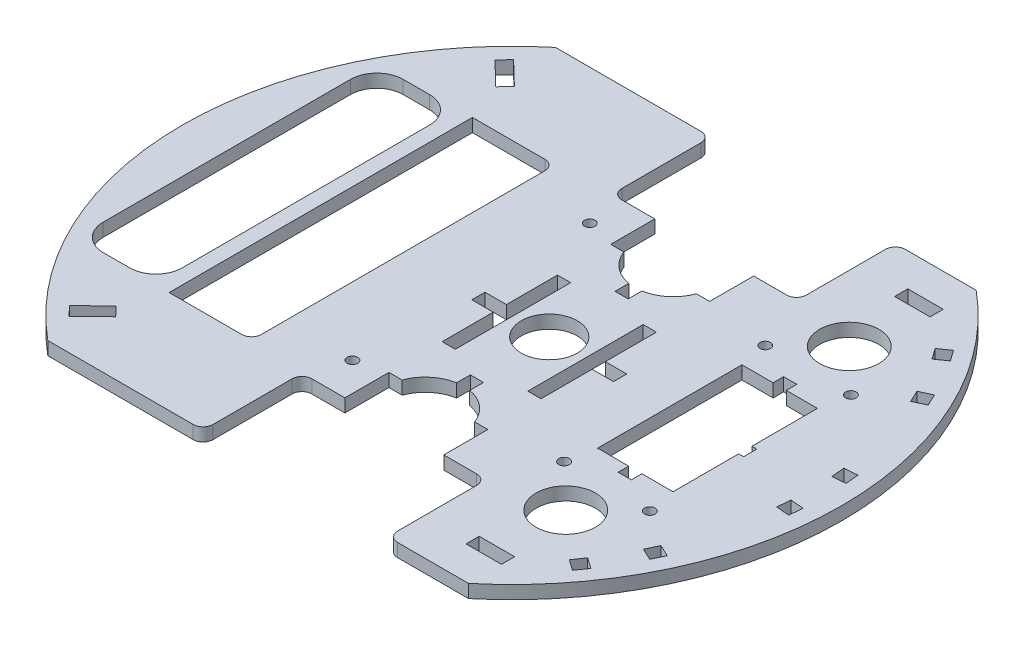
SolidWorks part; units mm, degrees
material "Oak"
ref_plane "Front Plane" through (0, 0, 0) normal (0, 0, 1) x (1, 0, 0)
ref_plane "Top Plane" through (0, 0, 0) normal (0, 1, 0) x (1, 0, 0)
ref_plane "Right Plane" through (0, 0, 0) normal (1, 0, 0) x (0, 0, -1)
sketch "Sketch1" plane through (0, 101.3337, 0) normal (0, 1, 0) x (1, 0, 0)
  line L0 (173.9372, -134.9612) -> (177.9372, -134.9612)
  line L2 (164.4872, -181.9612) -> (187.3872, -181.9612)
  line L3 (164.4872, -181.9612) -> (164.4872, -138.1612)
  line L12 (191.7991, -107.843) -> (195.0757, -105.5487)
  line L13 (189.5048, -104.5664) -> (191.7991, -107.843)
  line L14 (192.7814, -102.2721) -> (189.5048, -104.5664)
  line L15 (195.0757, -105.5487) -> (192.7814, -102.2721)
  line L16 (191.7991, -107.843) -> (195.0757, -105.5487)
  line L17 (189.5048, -104.5664) -> (191.7991, -107.843)
  line L18 (192.7814, -102.2721) -> (189.5048, -104.5664)
  line L19 (195.0757, -105.5487) -> (192.7814, -102.2721)
  line L28 (199.6807, -122.1917) -> (203.3059, -120.5012)
  line L29 (197.9902, -118.5664) -> (199.6807, -122.1917)
  line L30 (201.6155, -116.876) -> (197.9902, -118.5664)
  line L31 (203.3059, -120.5012) -> (201.6155, -116.876)
  line L32 (199.6807, -122.1917) -> (203.3059, -120.5012)
  line L33 (197.9902, -118.5664) -> (199.6807, -122.1917)
  line L34 (201.6155, -116.876) -> (197.9902, -118.5664)
  line L35 (203.3059, -120.5012) -> (201.6155, -116.876)
  line L68 (189.5048, -215.556) -> (192.7814, -217.8503)
  line L69 (191.7991, -212.2794) -> (189.5048, -215.556)
  line L70 (195.0757, -214.5737) -> (191.7991, -212.2794)
  line L71 (192.7814, -217.8503) -> (195.0757, -214.5737)
  line L72 (189.5048, -215.556) -> (192.7814, -217.8503)
  line L73 (191.7991, -212.2794) -> (189.5048, -215.556)
  line L74 (195.0757, -214.5737) -> (191.7991, -212.2794)
  line L75 (192.7814, -217.8503) -> (195.0757, -214.5737)
  line L84 (197.9902, -201.556) -> (201.6155, -203.2464)
  line L85 (199.6807, -197.9307) -> (197.9902, -201.556)
  line L86 (203.3059, -199.6212) -> (199.6807, -197.9307)
  line L87 (201.6155, -203.2464) -> (203.3059, -199.6212)
  line L88 (197.9902, -201.556) -> (201.6155, -203.2464)
  line L89 (199.6807, -197.9307) -> (197.9902, -201.556)
  line L90 (203.3059, -199.6212) -> (199.6807, -197.9307)
  line L91 (201.6155, -203.2464) -> (203.3059, -199.6212)
  line L116 (207.4498, -153.87) -> (211.4346, -153.5214)
  line L117 (207.1012, -149.8852) -> (207.4498, -153.87)
  line L118 (211.086, -149.5366) -> (207.1012, -149.8852)
  line L119 (211.4346, -153.5214) -> (211.086, -149.5366)
  line L120 (207.4498, -153.87) -> (211.4346, -153.5214)
  line L121 (207.1012, -149.8852) -> (207.4498, -153.87)
  line L122 (211.086, -149.5366) -> (207.1012, -149.8852)
  line L123 (211.4346, -153.5214) -> (211.086, -149.5366)
  line L124 (207.1012, -170.2372) -> (211.086, -170.5858)
  line L125 (207.4498, -166.2524) -> (207.1012, -170.2372)
  line L126 (211.4346, -166.601) -> (207.4498, -166.2524)
  line L127 (211.086, -170.5858) -> (211.4346, -166.601)
  line L128 (207.1012, -170.2372) -> (211.086, -170.5858)
  line L129 (207.4498, -166.2524) -> (207.1012, -170.2372)
  line L130 (211.4346, -166.601) -> (207.4498, -166.2524)
  line L131 (211.086, -170.5858) -> (211.4346, -166.601)
  line L256 (162.9372, -190.5612) -> (188.9372, -190.5612) construction
  line L257 (58.6296, -114.0612) -> (80.6296, -114.0612)
  line L258 (58.6296, -114.0612) -> (58.6296, -206.0612)
  line L259 (58.6296, -206.0612) -> (80.6296, -206.0612)
  line L260 (49.7, -227.4778) -> (56.8934, -220.5312)
  line L261 (46.9213, -224.6004) -> (49.7, -227.4778)
  line L262 (54.1147, -217.6539) -> (46.9213, -224.6004)
  line L263 (56.8934, -220.5312) -> (54.1147, -217.6539)
  line L268 (46.9213, -95.522) -> (54.1147, -102.4685)
  line L269 (49.7, -92.6446) -> (46.9213, -95.522)
  line L270 (56.8934, -99.5912) -> (49.7, -92.6446)
  line L271 (54.1147, -102.4685) -> (56.8934, -99.5912)
  line L272 (170.4372, -223.0612) -> (170.4372, -227.0612)
  line L273 (180.4372, -223.0612) -> (170.4372, -223.0612)
  line L274 (180.4372, -227.0612) -> (180.4372, -223.0612)
  line L275 (170.4372, -227.0612) -> (180.4372, -227.0612)
  line L276 (170.4372, -223.0612) -> (170.4372, -227.0612)
  line L277 (180.4372, -223.0612) -> (170.4372, -223.0612)
  line L278 (180.4372, -227.0612) -> (180.4372, -223.0612)
  line L279 (170.4372, -227.0612) -> (180.4372, -227.0612)
  line L280 (170.4372, -93.0612) -> (170.4372, -97.0612)
  line L281 (180.4372, -93.0612) -> (170.4372, -93.0612)
  line L282 (180.4372, -97.0612) -> (180.4372, -93.0612)
  line L283 (170.4372, -97.0612) -> (180.4372, -97.0612)
  line L284 (170.4372, -93.0612) -> (170.4372, -97.0612)
  line L285 (180.4372, -93.0612) -> (170.4372, -93.0612)
  line L286 (180.4372, -97.0612) -> (180.4372, -93.0612)
  line L287 (170.4372, -97.0612) -> (180.4372, -97.0612)
  line L288 (170.4372, -93.0612) -> (169.6872, -93.0612)
  line L299 (90.4372, -237.0612) -> (99.9372, -237.0612)
  line L302 (99.9372, -237.0612) -> (99.9372, -207.0612)
  line L303 (99.9372, -207.0612) -> (120.9039, -207.0612)
  line L336 (155.9372, -207.0612) -> (155.9372, -237.0612)
  line L352 (155.9372, -237.0612) -> (165.4372, -237.0612)
  line L353 (123.9372, -199.7112) -> (123.9372, -195.7112) construction
  line L354 (123.9372, -195.7112) -> (131.9372, -195.7112) construction
  line L355 (134.9705, -207.0612) -> (155.9372, -207.0612)
  line L356 (125.9372, -190.0112) -> (129.9372, -190.0112)
  line L357 (125.9372, -190.0112) -> (125.9372, -182.0112)
  line L358 (52.8284, -237.0612) -> (90.4372, -237.0612)
  line L359 (90.4372, -237.0612) -> (90.4372, -207.0612)
  line L360 (90.4372, -207.0612) -> (112.9372, -207.0612)
  line L361 (165.4372, -207.0612) -> (165.4372, -237.0612)
  line L362 (165.4372, -237.0612) -> (180.4372, -237.0612)
  line L363 (180.4372, -83.0612) -> (165.4372, -83.0612)
  line L364 (165.4372, -83.0612) -> (165.4372, -113.0612)
  line L365 (165.4372, -113.0612) -> (142.9372, -113.0612)
  line L366 (90.4372, -113.0612) -> (90.4372, -83.0612)
  line L367 (90.4372, -83.0612) -> (52.8284, -83.0612)
  line L368 (52.8284, -237.0612) -> (90.4372, -237.0612)
  line L369 (90.4372, -237.0612) -> (90.4372, -207.0612) construction
  line L370 (90.4372, -207.0612) -> (120.9039, -207.0612) construction
  line L371 (165.4372, -207.0612) -> (165.4372, -237.0612) construction
  line L372 (165.4372, -237.0612) -> (180.4372, -237.0612)
  line L373 (180.4372, -83.0612) -> (165.4372, -83.0612)
  line L374 (165.4372, -83.0612) -> (165.4372, -113.0612) construction
  line L375 (165.4372, -113.0612) -> (142.9372, -113.0612) construction
  line L376 (90.4372, -113.0612) -> (90.4372, -83.0612) construction
  line L377 (90.4372, -83.0612) -> (52.8284, -83.0612)
  line L378 (125.9372, -182.0112) -> (129.9372, -182.0112)
  line L379 (129.9372, -190.0112) -> (129.9372, -182.0112)
  line L380 (125.9372, -190.0112) -> (129.9372, -182.0112) construction
  line L381 (125.9372, -182.0112) -> (129.9372, -190.0112) construction
  line L382 (134.9705, -207.0612) -> (112.9372, -207.0612) construction
  line L383 (16.6328, -160.0612) -> (21.6328, -160.0612) construction
  line L384 (155.9372, -113.0612) -> (155.9372, -83.0612)
  line L385 (134.9705, -113.0612) -> (155.9372, -113.0612)
  line L386 (99.9372, -83.0612) -> (99.9372, -113.0612)
  line L387 (99.9372, -113.0612) -> (120.9039, -113.0612)
  line L388 (125.9372, -130.1112) -> (125.9372, -138.1112)
  line L389 (125.9372, -138.1112) -> (129.9372, -130.1112) construction
  line L390 (125.9372, -130.1112) -> (129.9372, -138.1112) construction
  line L391 (125.9372, -138.1112) -> (129.9372, -138.1112)
  line L392 (129.9372, -130.1112) -> (129.9372, -138.1112)
  line L393 (125.9372, -130.1112) -> (129.9372, -130.1112)
  line L394 (90.4372, -83.0612) -> (99.9372, -83.0612)
  line L395 (155.9372, -83.0612) -> (165.4372, -83.0612)
  line L396 (142.9372, -142.5612) -> (138.9372, -142.5612) construction
  line L397 (142.9372, -144.5612) -> (142.9372, -142.5612) construction
  line L398 (138.9372, -144.5612) -> (138.9372, -142.5612) construction
  line L400 (138.9372, -175.5612) -> (138.9372, -144.5612) construction
  line L401 (138.9372, -177.5612) -> (138.9372, -175.5612) construction
  line L402 (142.9372, -177.5612) -> (138.9372, -177.5612) construction
  line L403 (142.9372, -177.5612) -> (142.9372, -175.5612) construction
  line L404 (116.9372, -144.5612) -> (116.9372, -142.5612) construction
  line L405 (116.9372, -175.5612) -> (116.9372, -144.5612) construction
  line L406 (116.9372, -177.5612) -> (116.9372, -175.5612) construction
  line L407 (112.9372, -177.5612) -> (112.9372, -175.5612) construction
  line L409 (112.9372, -144.5612) -> (112.9372, -142.5612) construction
  line L410 (116.9372, -142.5612) -> (112.9372, -142.5612) construction
  line L411 (116.9372, -177.5612) -> (112.9372, -177.5612) construction
  line L412 (142.9372, -142.5612) -> (138.9372, -142.5612)
  line L413 (142.9372, -144.5612) -> (142.9372, -142.5612)
  line L414 (138.9372, -144.5612) -> (138.9372, -142.5612)
  line L416 (138.9372, -175.5612) -> (138.9372, -144.5612)
  line L417 (138.9372, -177.5612) -> (138.9372, -175.5612)
  line L418 (142.9372, -177.5612) -> (138.9372, -177.5612)
  line L419 (142.9372, -177.5612) -> (142.9372, -175.5612)
  line L420 (116.9372, -144.5612) -> (116.9372, -142.5612)
  line L421 (116.9372, -175.5612) -> (116.9372, -144.5612)
  line L422 (116.9372, -177.5612) -> (116.9372, -175.5612)
  line L423 (112.9372, -177.5612) -> (112.9372, -175.5612)
  line L425 (112.9372, -144.5612) -> (112.9372, -142.5612)
  line L426 (116.9372, -142.5612) -> (112.9372, -142.5612)
  line L427 (116.9372, -177.5612) -> (112.9372, -177.5612)
  line L432 (164.4872, -138.1612) -> (187.3872, -138.1612)
  line L433 (187.3872, -181.9612) -> (187.3872, -138.1612)
  line L446 (170.4372, -223.0612) -> (169.6872, -223.0612)
  line L447 (170.4372, -223.0612) -> (170.4372, -227.0612)
  line L448 (170.4372, -227.0612) -> (169.6872, -227.0612)
  line L449 (169.6872, -223.0612) -> (169.6872, -227.0612)
  line L450 (169.6872, -97.0612) -> (169.6872, -93.0612)
  line L451 (170.4372, -97.0612) -> (169.6872, -97.0612)
  line L452 (170.4372, -97.0612) -> (170.4372, -93.0612)
  line L456 (56.8934, -99.5912) -> (49.7, -92.6446)
  line L457 (164.4872, -181.9612) -> (187.3872, -138.1612) construction
  line L458 (164.4872, -138.1612) -> (187.3872, -181.9612) construction
  line L459 (173.9372, -181.9612) -> (177.9372, -181.9612)
  line L460 (173.9372, -181.9612) -> (173.9372, -185.1612)
  line L461 (173.9372, -185.1612) -> (177.9372, -185.1612)
  line L462 (177.9372, -181.9612) -> (177.9372, -185.1612)
  line L463 (177.9372, -138.1612) -> (177.9372, -134.9612)
  line L464 (173.9372, -138.1612) -> (177.9372, -138.1612)
  line L465 (173.9372, -138.1612) -> (173.9372, -134.9612)
  line L469 (37.1296, -114.6239) -> (47.1296, -114.6239)
  line L477 (30.1296, -160.0612) -> (216.6328, -160.0612) construction
  line L482 (83.6296, -203.0612) -> (83.6296, -117.0612)
  line L489 (104.2179, -124.0612) -> (104.2179, -196.0612) construction
  line L493 (187.3872, -158.0612) -> (188.8872, -158.0612)
  line L494 (187.3872, -158.0612) -> (187.3872, -162.0612)
  line L495 (187.3872, -162.0612) -> (188.8872, -162.0612)
  line L496 (188.8872, -158.0612) -> (188.8872, -162.0612)
  line L497 (112.9372, -158.0612) -> (106.4372, -158.0612)
  line L498 (112.9372, -158.0612) -> (112.9372, -162.0612)
  line L499 (112.9372, -162.0612) -> (106.4372, -162.0612)
  line L500 (106.4372, -158.0612) -> (106.4372, -162.0612)
  line L537 (142.9372, -193.7012) -> (142.9372, -207.0612)
  line L538 (142.9372, -193.7012) -> (142.9372, -207.0612)
  line L539 (142.9372, -207.0612) -> (165.4372, -207.0612)
  line L540 (142.9372, -207.0612) -> (165.4372, -207.0612)
  line L541 (142.9372, -113.0612) -> (142.9372, -126.4212)
  line L542 (142.9372, -113.0612) -> (142.9372, -126.4212)
  line L543 (142.9372, -126.4212) -> (138.9372, -126.4212)
  line L544 (142.9372, -126.4212) -> (138.9372, -126.4212)
  line L545 (138.9372, -126.4212) -> (138.9372, -113.0612)
  line L546 (138.9372, -126.4212) -> (138.9372, -113.0612)
  line L547 (138.9372, -113.0612) -> (116.9372, -113.0612)
  line L548 (138.9372, -113.0612) -> (116.9372, -113.0612)
  line L549 (116.9372, -113.0612) -> (116.9372, -126.4212)
  line L550 (116.9372, -113.0612) -> (116.9372, -126.4212)
  line L551 (116.9372, -126.4212) -> (112.9372, -126.4212)
  line L552 (116.9372, -126.4212) -> (112.9372, -126.4212)
  line L553 (112.9372, -126.4212) -> (112.9372, -113.0612)
  line L554 (112.9372, -126.4212) -> (112.9372, -113.0612)
  line L555 (112.9372, -113.0612) -> (90.4372, -113.0612)
  line L556 (112.9372, -113.0612) -> (90.4372, -113.0612)
  line L557 (112.9372, -207.0612) -> (112.9372, -193.7012)
  line L558 (112.9372, -207.0612) -> (112.9372, -193.7012)
  line L559 (112.9372, -193.7012) -> (116.9372, -193.7012)
  line L560 (112.9372, -193.7012) -> (116.9372, -193.7012)
  line L561 (116.9372, -193.7012) -> (116.9372, -207.0612)
  line L562 (116.9372, -193.7012) -> (116.9372, -207.0612)
  line L563 (116.9372, -207.0612) -> (138.9372, -207.0612)
  line L564 (116.9372, -207.0612) -> (138.9372, -207.0612)
  line L565 (138.9372, -207.0612) -> (138.9372, -193.7012)
  line L566 (138.9372, -207.0612) -> (138.9372, -193.7012)
  line L567 (138.9372, -193.7012) -> (142.9372, -193.7012)
  line L568 (138.9372, -193.7012) -> (142.9372, -193.7012)
  line L835 (112.9372, -175.5612) -> (112.9372, -144.5612) construction
  line L836 (112.9372, -175.5612) -> (112.9372, -144.5612)
  line L867 (142.9372, -175.5612) -> (142.9372, -144.5612) construction
  line L868 (142.9372, -175.5612) -> (142.9372, -144.5612)
  line L873 (142.9372, -162.0612) -> (149.4372, -162.0612)
  line L874 (142.9372, -158.0612) -> (142.9372, -162.0612)
  line L875 (149.4372, -158.0612) -> (142.9372, -158.0612)
  line L876 (149.4372, -162.0612) -> (149.4372, -158.0612)
  line L877 (142.9372, -162.0612) -> (149.4372, -162.0612)
  line L878 (142.9372, -158.0612) -> (142.9372, -162.0612)
  line L879 (149.4372, -158.0612) -> (142.9372, -158.0612)
  line L880 (149.4372, -162.0612) -> (149.4372, -158.0612)
  line L1351 (54.1296, -197.5612) -> (54.1296, -122.5612)
  line L1352 (46.1296, -114.5612) -> (38.1296, -114.5612)
  line L1353 (30.1296, -122.5612) -> (30.1296, -197.5612)
  line L1354 (38.1296, -205.5612) -> (46.1296, -205.5612)
  circle A0 centre (127.9372, -160.0612) radius 8.5
  circle A5 centre (127.9372, -160.0612) radius 5
  circle A6 centre (127.9372, -160.0612) radius 5 construction
  arc A7 (134.9705, -207.0612) -> (120.9039, -207.0612) centre (127.9372, -197.7112) ccw
  circle A8 centre (116.6328, -160.0612) radius 100 construction
  circle A9 centre (116.6328, -160.0612) radius 95 construction
  arc A13 (134.9705, -113.0612) -> (120.9039, -113.0612) centre (127.9372, -122.4112) cw
  circle A17 centre (175.9372, -203.0612) radius 9
  circle A19 centre (175.9372, -117.0612) radius 9
  arc A32 (180.4372, -237.0612) -> (180.4372, -83.0612) centre (116.6328, -160.0612) ccw
  arc A33 (52.8284, -83.0612) -> (52.8284, -237.0612) centre (116.6328, -160.0612) ccw
  arc A34 (180.4372, -237.0612) -> (180.4372, -83.0612) centre (116.6328, -160.0612) ccw
  arc A35 (52.8284, -83.0612) -> (52.8284, -237.0612) centre (116.6328, -160.0612) ccw
  arc A50 (54.1296, -122.5612) -> (46.1296, -114.5612) centre (46.1296, -122.5612) ccw
  arc A51 (54.1296, -197.5612) -> (46.1296, -205.5612) centre (46.1296, -197.5612) cw
  arc A52 (30.1296, -197.5612) -> (38.1296, -205.5612) centre (38.1296, -197.5612) ccw
  arc A53 (38.1296, -114.5612) -> (30.1296, -122.5612) centre (38.1296, -122.5612) ccw
  circle A65 centre (162.9372, -190.5612) radius 1.6
  circle A66 centre (188.9372, -190.5612) radius 1.6
  circle A67 centre (188.9372, -129.5612) radius 1.6
  circle A68 centre (162.9372, -129.5612) radius 1.6
  arc A69 (80.6296, -114.0612) -> (83.6296, -117.0612) centre (80.6296, -117.0612) cw
  arc A70 (80.6296, -206.0612) -> (83.6296, -203.0612) centre (80.6296, -203.0612) ccw
  circle A72 centre (104.2179, -196.0612) radius 1.6
  circle A118 centre (104.2179, -124.0612) radius 1.6
  point P33 (58.6296, -160.0612)
  point P68 (175.9372, -185.1612)
  point P70 (175.9372, -160.0612)
  point P85 (123.9372, -197.7112)
  point P88 (127.9372, -195.7112)
  point P89 (127.9372, -186.0112)
  point P113 (175.9372, -181.9612)
  point P117 (83.6296, -114.0612)
  point P125 (54.1296, -160.0612)
  point P140 (30.1296, -160.0612)
  point P163 (54.1296, -114.5612)
  point P165 (42.1296, -114.6239)
  point P166 (42.1296, -114.5612)
  point P179 (83.6296, -206.0612)
  point P180 (188.8872, -160.0612)
  point P188 (187.3872, -160.0612)
  point P200 (54.1296, -205.5612)
  point P241 (92.1295, -206.0264)
  point P246 (30.1296, -114.5612)
  point P251 (90.12, -148.0612)
  point P253 (104.2179, -160.0612)
  point P254 (78.6296, -114.0612)
  point P255 (106.4372, -160.0612)
  point P258 (97.6296, -114.0612)
  point P263 (175.9372, -190.5612)
  dimension "D18" = 17
  dimension "D22" = 23.4
  dimension "D26" = 4.5
  dimension "D27" = 18
  dimension "D39" = 3.2
  dimension "D48" = 4
  dimension "D58" = 44
  dimension "D56" = 5
  dimension "D60" = 8
  dimension "D54" = 92
  dimension "D63" = 1.5
  dimension "D62" = 23.7193
  dimension "D66" = 3.2
  dimension "D71" = 3.2
  dimension "D64" = 3
  dimension "D19" = 43.8
  dimension "D21" = 56
  dimension "D23" = 4
  dimension "D24" = 4
  dimension "D28" = 58
  dimension "D29" = 8.5
  dimension "D30" = 20
  dimension "D31" = 4
  dimension "D37" = 91
  dimension "D38" = 24
  dimension "D36" = 4
  dimension "D52" = 0.75
  dimension "D57" = 4
  dimension "D25" = 22.9
  dimension "D33" = 10
  dimension "D32" = 10
  dimension "D59" = 44
  dimension "D8" = 25
  dimension "D14" = 20
  dimension "D61" = 4
  dimension "D69" = 14
  dimension "D72" = 30.5
  dimension "D73" = 26
  dimension "D76" = 72
  dimension "D2" = 0
  dimension "D4" = 0
  dimension "D9" = 0
  dimension "D11" = 0
  dimension "D15" = 0
  dimension "D16" = 0
  dimension "D20" = 0
  dimension "D34" = 0
  dimension "D35" = 0
  dimension "D40" = 0
  dimension "D51" = 0
extrude "Boss-Extrude1" add sketch "Sketch1" along normal blind 4
fillet "Fillet2" radius 3 8 edges at (99.9372, 103.3337, 237.0612) (155.9372, 103.3337, 237.0612) (155.9372, 103.3337, 83.0612) (99.9372, 103.3337, 83.0612) (155.9372, 103.3337, 207.0612) (99.9372, 103.3337, 207.0612) (155.9372, 103.3337, 113.0612) (99.9372, 103.3337, 113.0612)
equation "\"WT\"=4"
equation "\"M3_hole\"= 3.2"
